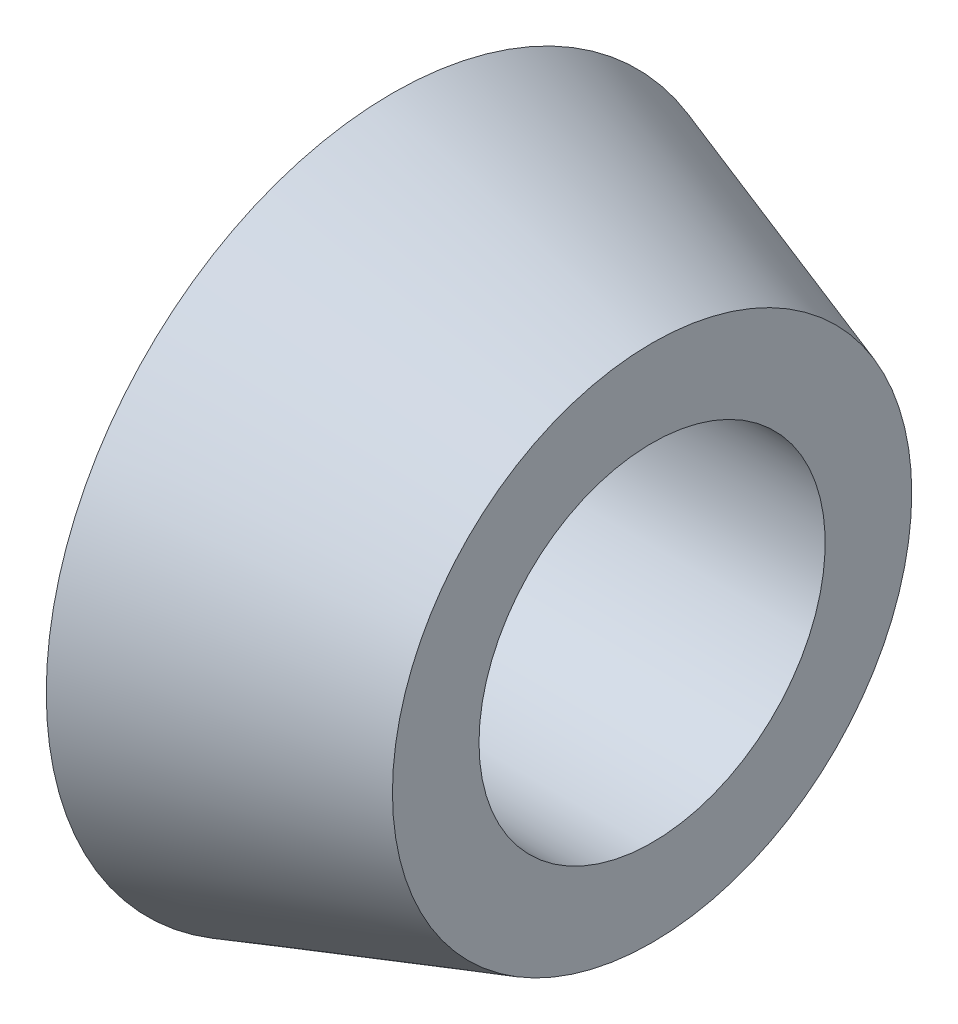
SolidWorks part; units mm, degrees
material "6061-T6 (SS)"
ref_plane "Płaszczyzna XY" through (0, 0, 0) normal (0, 0, 1) x (1, 0, 0)
ref_plane "Płaszczyzna XZ" through (0, 0, 0) normal (0, 1, 0) x (1, 0, 0)
ref_plane "Płaszczyzna YZ" through (0, 0, 0) normal (1, 0, 0) x (0, 0, -1)
sketch "Szkic1" plane through (0, 0, 0) normal (0, 0, 1) x (1, 0, 0)
  line L0 (0, 0) -> (7.6683, 0) construction
  line L1 (0, 3) -> (4.5, 3)
  line L2 (4.5, 3) -> (4.5, 4.5)
  line L3 (4.5, 4.5) -> (0, 6)
  line L5 (0, 6) -> (0, 3)
  dimension "D1" = 6
  dimension "D2" = 6
  dimension "D3" = 4.5
  dimension "D5" = 9
revolve "Obrót1" add sketch "Szkic1" angle 360 about L0
